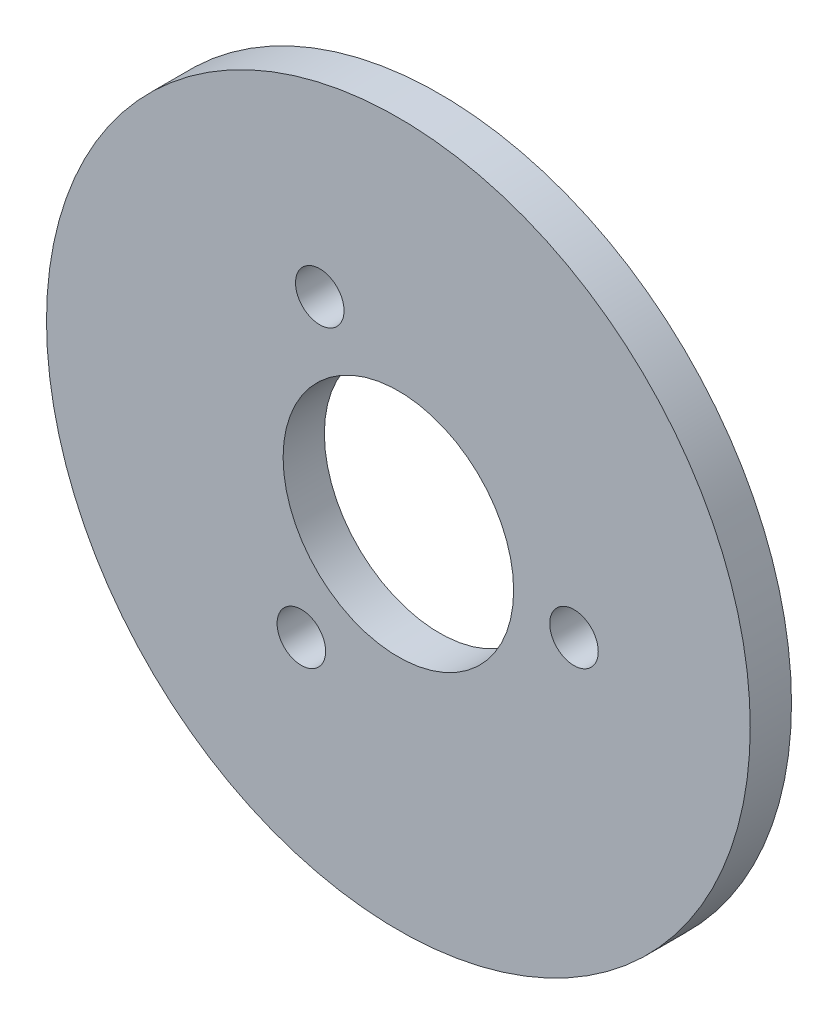
SolidWorks part; units mm, degrees
ref_plane "Front Plane" through (0, 0, 0) normal (0, 0, 1) x (1, 0, 0)
ref_plane "Top Plane" through (0, 0, 0) normal (0, 1, 0) x (1, 0, 0)
ref_plane "Right Plane" through (0, 0, 0) normal (1, 0, 0) x (0, 0, -1)
sketch "Sketch1" plane through (0, 0, 0) normal (0, 0, 1) x (1, 0, 0)
  circle A0 centre (0, 0) radius 29
  circle A1 centre (0, 0) radius 9.5
  circle A2 centre (0, 0) radius 14.5 construction
  circle A3 centre (-6.4782, 12.9724) radius 2
  circle A4 centre (14.4735, -0.8759) radius 2
  circle A5 centre (-7.9953, -12.0965) radius 2
  dimension "D1" = 58
  dimension "D2" = 19
  dimension "D3" = 5
  dimension "D4" = 4
  dimension "D5" = 3
extrude "Boss-Extrude1" add sketch "Sketch1" along normal blind 3.4
